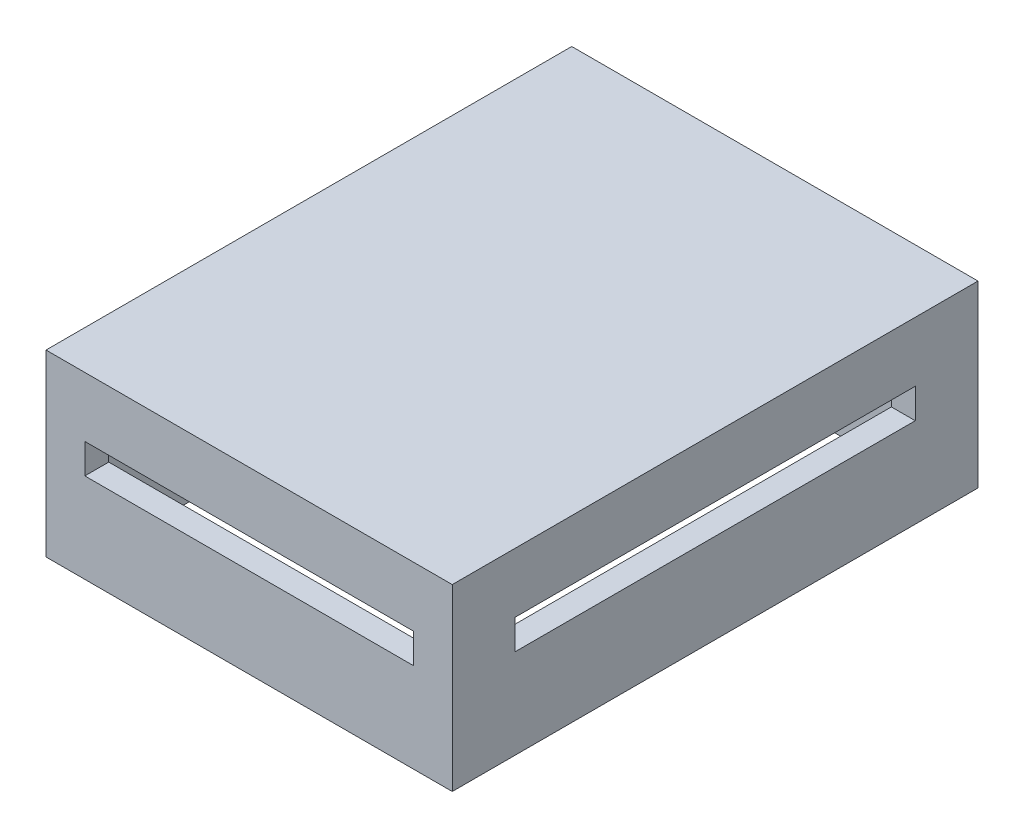
SolidWorks part; units mm, degrees
ref_plane "Front Plane" through (0, 0, 0) normal (0, 0, 1) x (1, 0, 0)
ref_plane "Top Plane" through (0, 0, 0) normal (0, 1, 0) x (1, 0, 0)
ref_plane "Right Plane" through (0, 0, 0) normal (1, 0, 0) x (0, 0, -1)
sketch "Croquis1" plane through (0, 0, 0) normal (0, 1, 0) x (1, 0, 0)
  line L0 (-4, -4) -> (-4, 84)
  line L1 (0, 0) -> (60, 0)
  line L2 (0, 0) -> (0, 80)
  line L3 (0, 80) -> (60, 80)
  line L4 (60, 0) -> (60, 80)
  line L5 (-4, 84) -> (64, 84)
  line L6 (64, -4) -> (64, 84)
  line L7 (-4, -4) -> (64, -4)
  dimension "D1" = 60
  dimension "D2" = 80
  dimension "D3" = 4
extrude "Saliente-Extruir1" add sketch "Croquis1" along normal blind 27
sketch "Croquis3" plane through (0, 27, 0) normal (0, 1, 0) x (1, 0, 0)
  line L0 (64, 84) -> (-4, 84) construction
  line L1 (-4, -4) -> (64, -4)
  line L2 (-4, -4) -> (-4, 84)
  line L3 (-4, 84) -> (64, 84)
  line L4 (64, -4) -> (64, 84)
  line L5 (64, -4) -> (64, 84) construction
extrude "Saliente-Extruir2" add sketch "Croquis3" along normal blind 3
sketch "Croquis4" plane through (-4, 0, 0) normal (-1, 0, 0) x (0, 0, 1)
  line L0 (-84, 30) -> (4, 30) construction
  line L1 (-73.5, 20) -> (-6.5, 20)
  line L2 (-73.5, 20) -> (-73.5, 15)
  line L3 (-73.5, 15) -> (-6.5, 15)
  line L4 (-6.5, 20) -> (-6.5, 15)
  line L7 (-84, 30) -> (-84, 0) construction
  line L9 (-6.5, 15) -> (4, 15) construction
  dimension "D1" = 10
  dimension "D2" = 5
  dimension "D3" = 67
  dimension "D4" = 10.5
extrude "Cortar-Extruir1" cut sketch "Croquis4" against normal through all
sketch "Croquis5" plane through (0, 0, 4) normal (0, 0, 1) x (1, 0, 0)
  line L1 (2.5, 15) -> (57.5, 15)
  line L2 (2.5, 15) -> (2.5, 20)
  line L3 (2.5, 20) -> (57.5, 20)
  line L4 (57.5, 15) -> (57.5, 20)
  line L10 (64, 30) -> (64, 0) construction
  line L13 (-4, 20) -> (2.5, 20) construction
  line L14 (-4, 20) -> (-4, 15) construction
  line L15 (-4, 0) -> (64, 0) construction
  dimension "D1" = 55
  dimension "D2" = 6.5
  dimension "D3" = 15
  dimension "D4" = 20
extrude "Cortar-Extruir2" cut sketch "Croquis5" against normal through all
